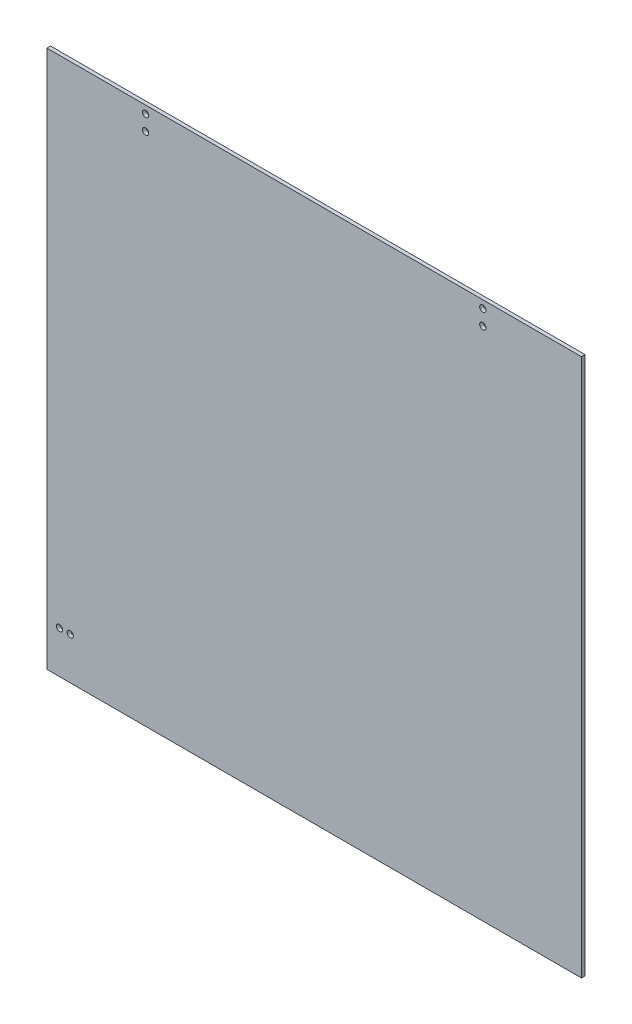
SolidWorks part; units mm, degrees
ref_plane "Front Plane" through (0, 0, 0) normal (0, 0, 1) x (1, 0, 0)
ref_plane "Top Plane" through (0, 0, 0) normal (0, 1, 0) x (1, 0, 0)
ref_plane "Right Plane" through (0, 0, 0) normal (1, 0, 0) x (0, 0, -1)
sketch "Sketch1" plane through (0, 0, 0) normal (0, 0, 1) x (1, 0, 0)
  line L1 (0, 0) -> (298, 0)
  line L2 (0, 0) -> (0, 300)
  line L3 (0, 300) -> (298, 300)
  line L4 (298, 0) -> (298, 300)
  dimension "D1" = 298
  dimension "D2" = 300
extrude "Boss-Extrude1" add sketch "Sketch1" along normal blind 2
sketch "Sketch2" plane through (0, 0, 2) normal (0, 0, 1) x (1, 0, 0)
  line L0 (298, 300) -> (0, 300) construction
  line L1 (298, 0) -> (298, 300) construction
  circle A0 centre (243, 295.75) radius 1.75
  circle A1 centre (243, 287.25) radius 1.75
  dimension "D1" = 3.5
  dimension "D4" = 3.5
  dimension "D2" = 4.25
  dimension "D3" = 55
  dimension "D5" = 12.75
  dimension "D6" = 55
extrude "Cut-Extrude1" cut sketch "Sketch2" against normal blind 20
sketch "Sketch3" plane through (0, 0, 2) normal (0, 0, 1) x (1, 0, 0)
  line L0 (0, 300) -> (0, 0) construction
  line L1 (298, 300) -> (0, 300) construction
  circle A0 centre (55, 287.25) radius 1.75
  circle A1 centre (55, 295.75) radius 1.75
  dimension "D1" = 3.5
  dimension "D4" = 3.5
  dimension "D2" = 55
  dimension "D3" = 12.75
  dimension "D5" = 4.25
  dimension "D6" = 55
extrude "Cut-Extrude2" cut sketch "Sketch3" against normal through all both and the other way through all
sketch "Sketch5" plane through (0, 0, 2) normal (0, 0, 1) x (1, 0, 0)
  line L0 (0, 0) -> (298, 0) construction
  line L1 (0, 300) -> (0, 0) construction
  circle A0 centre (7, 23.5) radius 1.75
  circle A1 centre (13, 23.5) radius 1.75
  dimension "D1" = 3.5
  dimension "D2" = 3.5
  dimension "D3" = 23.5
  dimension "D4" = 7
  dimension "D5" = 13
  dimension "D6" = 23.5
extrude "Cut-Extrude3" cut sketch "Sketch5" against normal through all
